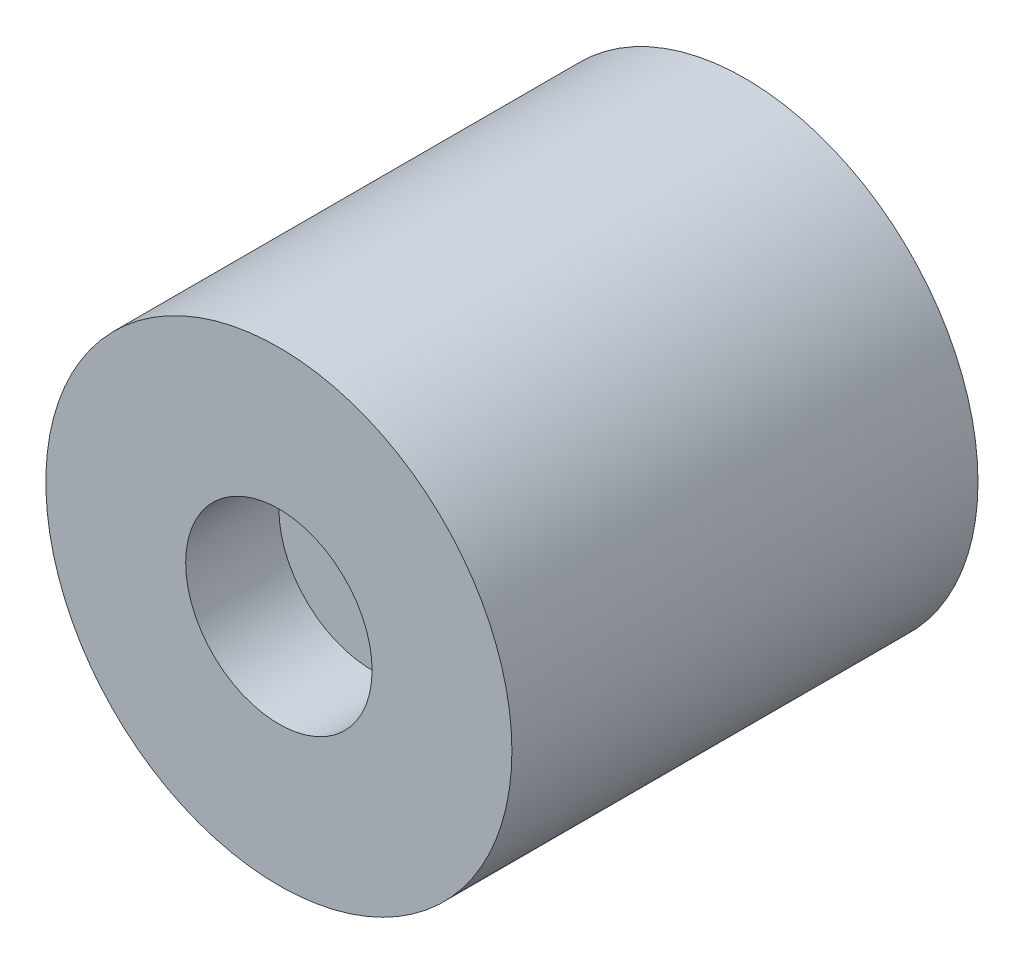
SolidWorks part; units mm, degrees
ref_plane "Plan de face" through (0, 0, 0) normal (0, 0, 1) x (1, 0, 0)
ref_plane "Plan de dessus" through (0, 0, 0) normal (0, 1, 0) x (1, 0, 0)
ref_plane "Plan de droite" through (0, 0, 0) normal (1, 0, 0) x (0, 0, -1)
sketch "Esquisse1" plane through (0, 0, 0) normal (0, 0, 1) x (1, 0, 0)
  circle A0 centre (0, 0) radius 12.5
  dimension "D1" = 25
extrude "Boss.-Extru.1" add sketch "Esquisse1" along normal blind 25
sketch "Esquisse3" plane through (0, 0, 25) normal (0, 0, 1) x (1, 0, 0)
  circle A0 centre (0, 0) radius 5
  dimension "D1" = 10
extrude "Enlèv. mat.-Extru.1" cut sketch "Esquisse3" against normal blind 5
